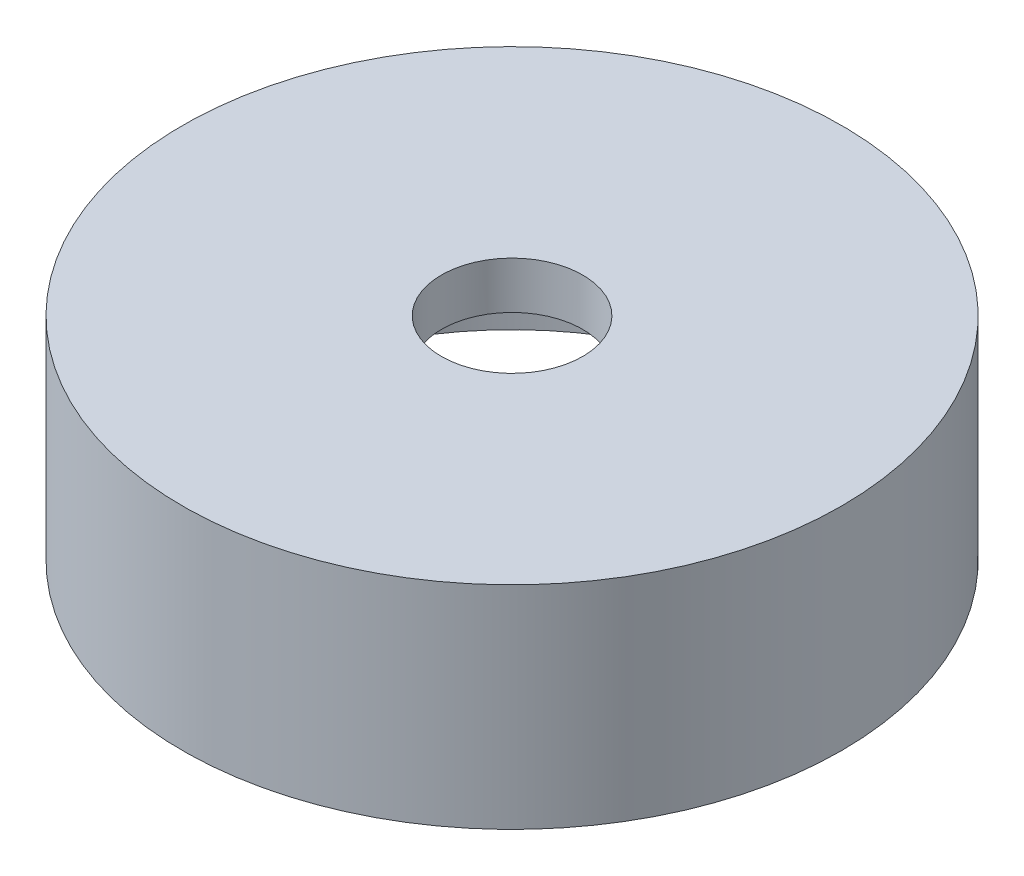
SolidWorks part; units mm, degrees
material "Alloy Steel (SS)"
ref_plane "Front Plane" through (0, 0, 0) normal (0, 0, 1) x (1, 0, 0)
ref_plane "Top Plane" through (0, 0, 0) normal (0, 1, 0) x (1, 0, 0)
ref_plane "Right Plane" through (0, 0, 0) normal (1, 0, 0) x (0, 0, -1)
sketch "Sketch1" plane through (0, 0, 0) normal (0, 0, 1) x (1, 0, 0)
  line L0 (0, 0) -> (0, 4.5) construction
  line L1 (0, 4.5) -> (7, 4.5)
  line L2 (7, 4.5) -> (7, 0)
  line L3 (0, 3.5) -> (6, 3.5)
  line L4 (6, 3.5) -> (6, 0)
  line L5 (0, 4.5) -> (0, 3.5)
  line L6 (6, 0) -> (7, 0)
  dimension "D1" = 7
  dimension "D2" = 4.5
  dimension "D3" = 1
revolve "Revolve1" add sketch "Sketch1" angle 360 about L0
hole_wizard "Ø3.0mm Dowel Hole1" positions "Sketch3" profile "Sketch4" hole size "Ø3.0" standard "ISO"
sketch "Sketch3" plane through (0, 4.5, 0) normal (0, 1, 0) x (1, 0, 0)
  point P0 (0, 0)
sketch "Sketch4" plane through (0, 4.5, 0) normal (1, 0, 0) x (0, 0, 1)
  line L0 (0, 0) -> (0, 8.5)
  line L1 (0, 8.5) -> (1.5, 7.5987)
  line L2 (1.5, 7.5987) -> (1.5, 0)
  line L5 (1.5, 0) -> (0, 0)
  line L10 (0, 8.5) -> (-1.5, 7.5987) construction
  line L11 (0, -6.35) -> (0, 107.95) construction
  dimension "Hole Dia." = 3
  dimension "Hole Depth" = 8.5
  dimension "Drill Angle" = 118
